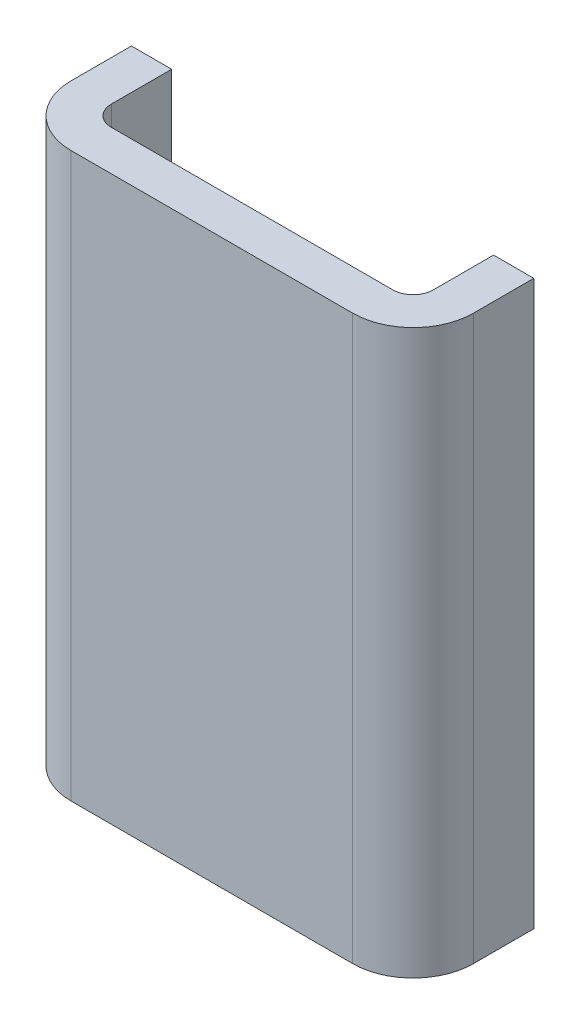
SolidWorks part; units mm, degrees
material "PLA"
ref_plane "Front Plane" through (0, 0, 0) normal (0, 0, 1) x (1, 0, 0)
ref_plane "Top Plane" through (0, 0, 0) normal (0, 1, 0) x (1, 0, 0)
ref_plane "Right Plane" through (0, 0, 0) normal (1, 0, 0) x (0, 0, -1)
sketch "Sketch1" plane through (0, 0, 0) normal (0, 1, 0) x (1, 0, 0)
  line L0 (0, 6.985) -> (0, 2.54)
  line L1 (2.54, 0) -> (60.96, 0)
  line L3 (2.54, 9.525) -> (60.96, 9.525)
  line L4 (63.5, 2.54) -> (63.5, 6.985)
  line L5 (-3.175, 6.985) -> (-3.175, 2.54)
  line L6 (2.54, -3.175) -> (60.96, -3.175)
  line L7 (66.675, 2.54) -> (66.675, 6.985)
  line L8 (2.54, 12.7) -> (60.96, 12.7)
  line L9 (2.54, 12.7) -> (-3.175, 12.7)
  line L10 (-3.175, 12.7) -> (-3.175, 6.985)
  line L11 (60.96, 12.7) -> (66.675, 12.7)
  line L12 (66.675, 12.7) -> (66.675, 6.985)
  arc A0 (60.96, 9.525) -> (63.5, 6.985) centre (60.96, 6.985) cw
  arc A1 (60.96, 0) -> (63.5, 2.54) centre (60.96, 2.54) ccw
  arc A2 (0, 2.54) -> (2.54, 0) centre (2.54, 2.54) ccw
  arc A3 (0, 6.985) -> (2.54, 9.525) centre (2.54, 6.985) cw
  arc A4 (-3.175, 2.54) -> (2.54, -3.175) centre (2.54, 2.54) ccw
  arc A5 (60.96, -3.175) -> (66.675, 2.54) centre (60.96, 2.54) ccw
  arc A8 (-3.175, 6.985) -> (2.54, 12.7) centre (2.54, 6.985) cw construction
  arc A9 (60.96, 12.7) -> (66.675, 6.985) centre (60.96, 6.985) cw construction
  point P7 (63.5, 9.525)
  point P10 (63.5, 0)
  point P13 (0, 0)
  dimension "D3" = 2.54
  dimension "D4" = 3.175
  dimension "D1" = 63.5
  dimension "D2" = 9.525
sketch "Sketch2" plane through (0, 0, 0) normal (0, 1, 0) x (1, 0, 0)
  line L1 (0, 0) -> (50.8, 0)
  line L2 (0, 0) -> (0, 12.7)
  line L3 (0, 12.7) -> (50.8, 12.7)
  line L4 (50.8, 0) -> (50.8, 12.7)
  dimension "D1" = 50.8
  dimension "D2" = 12.7
extrude "Boss-Extrude1" add sketch "Sketch2" along normal blind 88.9
fillet "Fillet2" radius 3.175 2 edges at (50.8, 44.45, 0) (0, 44.45, 0)
shell "Shell1" thickness 6.35
